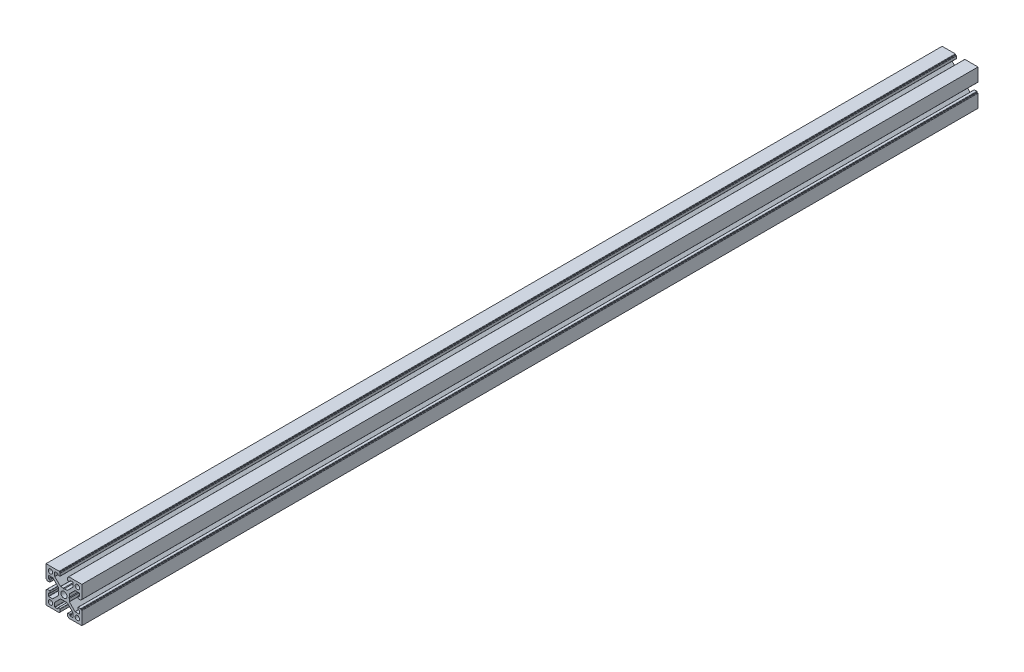
SolidWorks part; units mm, degrees
material "6063 T5"
ref_plane "Спереди" through (0, 0, 0) normal (0, 0, 1) x (1, 0, 0)
ref_plane "Сверху" through (0, 0, 0) normal (0, 1, 0) x (1, 0, 0)
ref_plane "Справа" through (0, 0, 0) normal (1, 0, 0) x (0, 0, -1)
sketch "Эскиз2" plane through (0, 0, 0) normal (0, 0, 1) x (1, 0, 0)
  line L0 (-20, 10.25) -> (-20, 20)
  line L1 (-20, 20) -> (-10.25, 20)
  line L2 (20, 20) -> (20, 10.25)
  line L3 (10.25, 20) -> (20, 20)
  line L4 (20, -20) -> (10.25, -20)
  line L5 (20, -10.25) -> (20, -20)
  line L6 (-20, -20) -> (-20, -10.25)
  line L7 (-10.25, -20) -> (-20, -20)
  circle A0 centre (0, 0) radius 3.4
  circle A1 centre (-15, 15) radius 2.45
  circle A2 centre (15, 15) radius 2.45
  circle A3 centre (15, -15) radius 2.45
  circle A4 centre (-15, -15) radius 2.45
  point P14 (0, 0)
  point P27 (0, 0)
  line B0 (-20, 10.25) -> (-20, 5.4)
  line B1 (-19.7, 5.1) -> (-19, 5.1)
  line B2 (-19, 5.1) -> (-19, 4.4)
  line B3 (-18.7, 4.1) -> (-16, 4.1)
  line B4 (-15.7, 4.4) -> (-15.7, 6.3)
  line B5 (-16, 6.6) -> (-16.9, 6.6)
  line B6 (-17.2, 6.9) -> (-17.2, 9.95)
  line B7 (-16.9, 10.25) -> (-12.5743, 10.25)
  line B8 (-12.3621, 10.1621) -> (-6.0879, 3.8879)
  line B9 (-6, 3.6757) -> (-6, 0.6)
  line B10 (-6, 0) -> (-20, 0) construction
  line B11 (-12.3621, -10.1621) -> (-6.0879, -3.8879)
  line B12 (-16.9, -10.25) -> (-12.5743, -10.25)
  line B13 (-17.2, -6.9) -> (-17.2, -9.95)
  line B14 (-16, -6.6) -> (-16.9, -6.6)
  line B15 (-15.7, -4.4) -> (-15.7, -6.3)
  line B16 (-18.7, -4.1) -> (-16, -4.1)
  line B17 (-19, -5.1) -> (-19, -4.4)
  line B18 (-19.7, -5.1) -> (-19, -5.1)
  line B19 (-20, -10.25) -> (-20, -5.4)
  line B20 (-6, 0.6) -> (-5.4, 0)
  line B21 (-5.4, 0) -> (-6, -0.6)
  line B22 (-6, -0.6) -> (-6, -3.6757)
  arc B23 (-15.7, 6.3) -> (-16, 6.6) centre (-16, 6.3) ccw
  arc B24 (-16, 4.1) -> (-15.7, 4.4) centre (-16, 4.4) ccw
  arc B25 (-19, 4.4) -> (-18.7, 4.1) centre (-18.7, 4.4) ccw
  arc B26 (-20, 5.4) -> (-19.7, 5.1) centre (-19.7, 5.4) ccw
  arc B27 (-6.0879, 3.8879) -> (-6, 3.6757) centre (-6.3, 3.6757) cw
  arc B28 (-12.5743, 10.25) -> (-12.3621, 10.1621) centre (-12.5743, 9.95) cw
  arc B29 (-17.2, 9.95) -> (-16.9, 10.25) centre (-16.9, 9.95) cw
  arc B30 (-16.9, 6.6) -> (-17.2, 6.9) centre (-16.9, 6.9) cw
  arc B31 (-16.9, -6.6) -> (-17.2, -6.9) centre (-16.9, -6.9) ccw
  arc B32 (-17.2, -9.95) -> (-16.9, -10.25) centre (-16.9, -9.95) ccw
  arc B33 (-12.5743, -10.25) -> (-12.3621, -10.1621) centre (-12.5743, -9.95) ccw
  arc B34 (-6.0879, -3.8879) -> (-6, -3.6757) centre (-6.3, -3.6757) ccw
  arc B35 (-20, -5.4) -> (-19.7, -5.1) centre (-19.7, -5.4) cw
  arc B36 (-19, -4.4) -> (-18.7, -4.1) centre (-18.7, -4.4) cw
  arc B37 (-16, -4.1) -> (-15.7, -4.4) centre (-16, -4.4) cw
  arc B38 (-15.7, -6.3) -> (-16, -6.6) centre (-16, -6.3) cw
  line B39 (10.25, 20) -> (5.4, 20)
  line B40 (5.1, 19.7) -> (5.1, 19)
  line B41 (5.1, 19) -> (4.4, 19)
  line B42 (4.1, 18.7) -> (4.1, 16)
  line B43 (4.4, 15.7) -> (6.3, 15.7)
  line B44 (6.6, 16) -> (6.6, 16.9)
  line B45 (6.9, 17.2) -> (9.95, 17.2)
  line B46 (10.25, 16.9) -> (10.25, 12.5743)
  line B47 (10.1621, 12.3621) -> (3.8879, 6.0879)
  line B48 (3.6757, 6) -> (0.6, 6)
  line B49 (0, 6) -> (0, 20) construction
  line B50 (-10.1621, 12.3621) -> (-3.8879, 6.0879)
  line B51 (-10.25, 16.9) -> (-10.25, 12.5743)
  line B52 (-6.9, 17.2) -> (-9.95, 17.2)
  line B53 (-6.6, 16) -> (-6.6, 16.9)
  line B54 (-4.4, 15.7) -> (-6.3, 15.7)
  line B55 (-4.1, 18.7) -> (-4.1, 16)
  line B56 (-5.1, 19) -> (-4.4, 19)
  line B57 (-5.1, 19.7) -> (-5.1, 19)
  line B58 (-10.25, 20) -> (-5.4, 20)
  line B59 (0.6, 6) -> (0, 5.4)
  line B60 (0, 5.4) -> (-0.6, 6)
  line B61 (-0.6, 6) -> (-3.6757, 6)
  arc B62 (6.3, 15.7) -> (6.6, 16) centre (6.3, 16) ccw
  arc B63 (4.1, 16) -> (4.4, 15.7) centre (4.4, 16) ccw
  arc B64 (4.4, 19) -> (4.1, 18.7) centre (4.4, 18.7) ccw
  arc B65 (5.4, 20) -> (5.1, 19.7) centre (5.4, 19.7) ccw
  arc B66 (3.8879, 6.0879) -> (3.6757, 6) centre (3.6757, 6.3) cw
  arc B67 (10.25, 12.5743) -> (10.1621, 12.3621) centre (9.95, 12.5743) cw
  arc B68 (9.95, 17.2) -> (10.25, 16.9) centre (9.95, 16.9) cw
  arc B69 (6.6, 16.9) -> (6.9, 17.2) centre (6.9, 16.9) cw
  arc B70 (-6.6, 16.9) -> (-6.9, 17.2) centre (-6.9, 16.9) ccw
  arc B71 (-9.95, 17.2) -> (-10.25, 16.9) centre (-9.95, 16.9) ccw
  arc B72 (-10.25, 12.5743) -> (-10.1621, 12.3621) centre (-9.95, 12.5743) ccw
  arc B73 (-3.8879, 6.0879) -> (-3.6757, 6) centre (-3.6757, 6.3) ccw
  arc B74 (-5.4, 20) -> (-5.1, 19.7) centre (-5.4, 19.7) cw
  arc B75 (-4.4, 19) -> (-4.1, 18.7) centre (-4.4, 18.7) cw
  arc B76 (-4.1, 16) -> (-4.4, 15.7) centre (-4.4, 16) cw
  arc B77 (-6.3, 15.7) -> (-6.6, 16) centre (-6.3, 16) cw
  line B78 (20, -10.25) -> (20, -5.4)
  line B79 (19.7, -5.1) -> (19, -5.1)
  line B80 (19, -5.1) -> (19, -4.4)
  line B81 (18.7, -4.1) -> (16, -4.1)
  line B82 (15.7, -4.4) -> (15.7, -6.3)
  line B83 (16, -6.6) -> (16.9, -6.6)
  line B84 (17.2, -6.9) -> (17.2, -9.95)
  line B85 (16.9, -10.25) -> (12.5743, -10.25)
  line B86 (12.3621, -10.1621) -> (6.0879, -3.8879)
  line B87 (6, -3.6757) -> (6, -0.6)
  line B88 (6, 0) -> (20, 0) construction
  line B89 (12.3621, 10.1621) -> (6.0879, 3.8879)
  line B90 (16.9, 10.25) -> (12.5743, 10.25)
  line B91 (17.2, 6.9) -> (17.2, 9.95)
  line B92 (16, 6.6) -> (16.9, 6.6)
  line B93 (15.7, 4.4) -> (15.7, 6.3)
  line B94 (18.7, 4.1) -> (16, 4.1)
  line B95 (19, 5.1) -> (19, 4.4)
  line B96 (19.7, 5.1) -> (19, 5.1)
  line B97 (20, 10.25) -> (20, 5.4)
  line B98 (6, -0.6) -> (5.4, 0)
  line B99 (5.4, 0) -> (6, 0.6)
  line B100 (6, 0.6) -> (6, 3.6757)
  arc B101 (15.7, -6.3) -> (16, -6.6) centre (16, -6.3) ccw
  arc B102 (16, -4.1) -> (15.7, -4.4) centre (16, -4.4) ccw
  arc B103 (19, -4.4) -> (18.7, -4.1) centre (18.7, -4.4) ccw
  arc B104 (20, -5.4) -> (19.7, -5.1) centre (19.7, -5.4) ccw
  arc B105 (6.0879, -3.8879) -> (6, -3.6757) centre (6.3, -3.6757) cw
  arc B106 (12.5743, -10.25) -> (12.3621, -10.1621) centre (12.5743, -9.95) cw
  arc B107 (17.2, -9.95) -> (16.9, -10.25) centre (16.9, -9.95) cw
  arc B108 (16.9, -6.6) -> (17.2, -6.9) centre (16.9, -6.9) cw
  arc B109 (16.9, 6.6) -> (17.2, 6.9) centre (16.9, 6.9) ccw
  arc B110 (17.2, 9.95) -> (16.9, 10.25) centre (16.9, 9.95) ccw
  arc B111 (12.5743, 10.25) -> (12.3621, 10.1621) centre (12.5743, 9.95) ccw
  arc B112 (6.0879, 3.8879) -> (6, 3.6757) centre (6.3, 3.6757) ccw
  arc B113 (20, 5.4) -> (19.7, 5.1) centre (19.7, 5.4) cw
  arc B114 (19, 4.4) -> (18.7, 4.1) centre (18.7, 4.4) cw
  arc B115 (16, 4.1) -> (15.7, 4.4) centre (16, 4.4) cw
  arc B116 (15.7, 6.3) -> (16, 6.6) centre (16, 6.3) cw
  line B117 (-10.25, -20) -> (-5.4, -20)
  line B118 (-5.1, -19.7) -> (-5.1, -19)
  line B119 (-5.1, -19) -> (-4.4, -19)
  line B120 (-4.1, -18.7) -> (-4.1, -16)
  line B121 (-4.4, -15.7) -> (-6.3, -15.7)
  line B122 (-6.6, -16) -> (-6.6, -16.9)
  line B123 (-6.9, -17.2) -> (-9.95, -17.2)
  line B124 (-10.25, -16.9) -> (-10.25, -12.5743)
  line B125 (-10.1621, -12.3621) -> (-3.8879, -6.0879)
  line B126 (-3.6757, -6) -> (-0.6, -6)
  line B127 (0, -6) -> (0, -20) construction
  line B128 (10.1621, -12.3621) -> (3.8879, -6.0879)
  line B129 (10.25, -16.9) -> (10.25, -12.5743)
  line B130 (6.9, -17.2) -> (9.95, -17.2)
  line B131 (6.6, -16) -> (6.6, -16.9)
  line B132 (4.4, -15.7) -> (6.3, -15.7)
  line B133 (4.1, -18.7) -> (4.1, -16)
  line B134 (5.1, -19) -> (4.4, -19)
  line B135 (5.1, -19.7) -> (5.1, -19)
  line B136 (10.25, -20) -> (5.4, -20)
  line B137 (-0.6, -6) -> (0, -5.4)
  line B138 (0, -5.4) -> (0.6, -6)
  line B139 (0.6, -6) -> (3.6757, -6)
  arc B140 (-6.3, -15.7) -> (-6.6, -16) centre (-6.3, -16) ccw
  arc B141 (-4.1, -16) -> (-4.4, -15.7) centre (-4.4, -16) ccw
  arc B142 (-4.4, -19) -> (-4.1, -18.7) centre (-4.4, -18.7) ccw
  arc B143 (-5.4, -20) -> (-5.1, -19.7) centre (-5.4, -19.7) ccw
  arc B144 (-3.8879, -6.0879) -> (-3.6757, -6) centre (-3.6757, -6.3) cw
  arc B145 (-10.25, -12.5743) -> (-10.1621, -12.3621) centre (-9.95, -12.5743) cw
  arc B146 (-9.95, -17.2) -> (-10.25, -16.9) centre (-9.95, -16.9) cw
  arc B147 (-6.6, -16.9) -> (-6.9, -17.2) centre (-6.9, -16.9) cw
  arc B148 (6.6, -16.9) -> (6.9, -17.2) centre (6.9, -16.9) ccw
  arc B149 (9.95, -17.2) -> (10.25, -16.9) centre (9.95, -16.9) ccw
  arc B150 (10.25, -12.5743) -> (10.1621, -12.3621) centre (9.95, -12.5743) ccw
  arc B151 (3.8879, -6.0879) -> (3.6757, -6) centre (3.6757, -6.3) ccw
  arc B152 (5.4, -20) -> (5.1, -19.7) centre (5.4, -19.7) cw
  arc B153 (4.4, -19) -> (4.1, -18.7) centre (4.4, -18.7) cw
  arc B154 (4.1, -16) -> (4.4, -15.7) centre (4.4, -16) cw
  arc B155 (6.3, -15.7) -> (6.6, -16) centre (6.3, -16) cw
  dimension "D1" = 6.8
  dimension "D3" = 4.9
  dimension "D4" = 15
  dimension "D5" = 15
  dimension "D2" = 20
  dimension "D7" = 4
  dimension "D6" = 4
sketch_block_instance "8B(20,5PL_cut)-4"
sketch_block "8B(20,5PL_cut)" parameters "D7"=0.3, "D8"=0.3, "D12"=0.3, "D1"=14, "D2"=4.3, "D3"=8.2, "D4"=20.5, "D5"=10.2, "D6"=135, "D9"=1, "D10"=2.5, "D11"=1.5, "D13"=1.2, "D14"=11.8
sketch_block_instance "8B(20,5PL_cut)-6"
sketch_block_instance "8B(20,5PL_cut)-7"
sketch_block_instance "8B(20,5PL_cut)-8"
extrude "Бобышка-Вытянуть1" add sketch "Эскиз2" along normal blind 1000 contours B155 B132 B154 B133 B153 B134 B135 B152 B136 L4 L5 B78 B104 B79 B80 B103 B81 B102 B82 B101 B83 B108 B84 B107 B85 B106 B86 B105 B87 B98 B99 B100 B112 B89 B111 B90 B110 B91 B109 B92 B116 B93 B115 B94 B114 B95 B96 B113 B97 L2 L3
